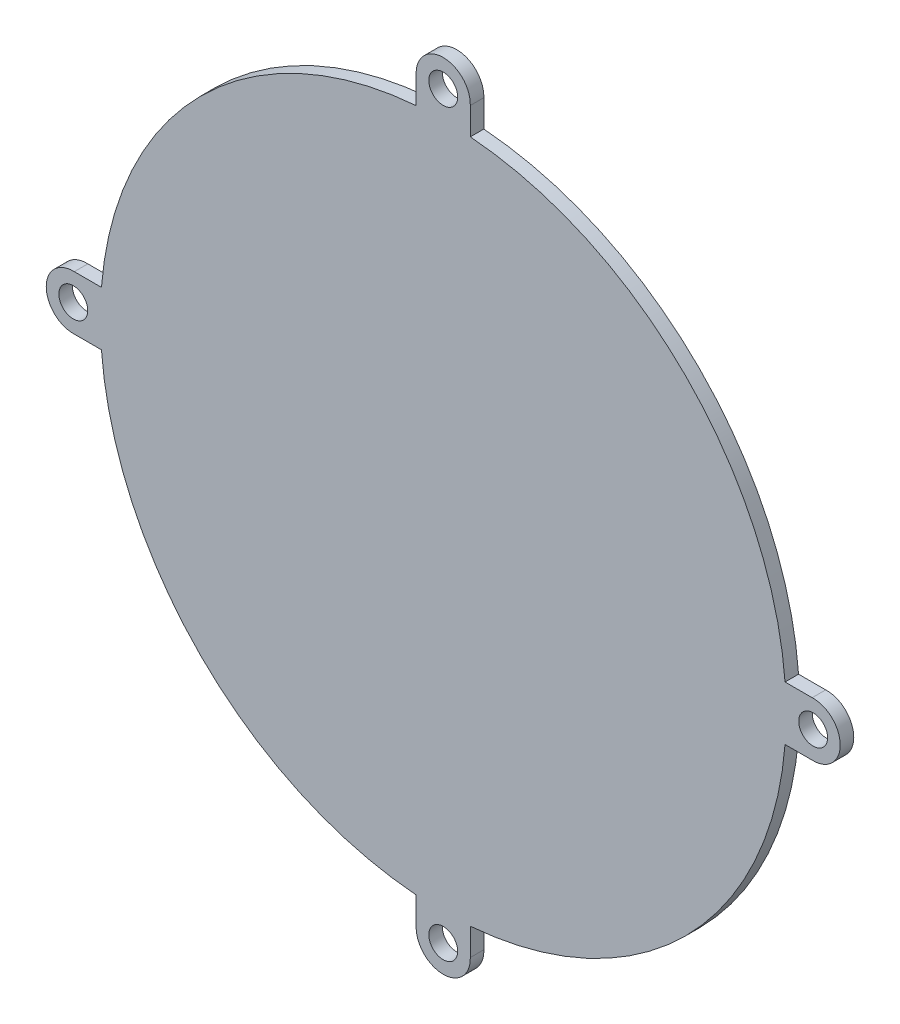
SolidWorks part; units mm, degrees
ref_plane "Front" through (0, 0, 0) normal (0, 0, 1) x (1, 0, 0)
ref_plane "Top" through (0, 0, 0) normal (0, 1, 0) x (1, 0, 0)
ref_plane "Right" through (0, 0, 0) normal (1, 0, 0) x (0, 0, -1)
sketch "Sketch1" plane through (0, 0, 0) normal (0, 0, 1) x (1, 0, 0)
  line L0 (-40.8902, 2.998) -> (-37.8816, 2.998)
  line L1 (40.8902, -2.998) -> (37.8816, -2.998)
  line L2 (-2.998, -40.8902) -> (-2.998, -37.8816)
  line L3 (2.998, 40.8902) -> (2.998, 37.8816)
  line L4 (-37.8816, -2.998) -> (-40.8902, -2.998)
  line L6 (-2.998, 37.8816) -> (-2.998, 40.8902)
  line L8 (37.8816, 2.998) -> (40.8902, 2.998)
  line L10 (2.998, -37.8816) -> (2.998, -40.8902)
  arc A1 (-37.8816, -2.998) -> (-2.998, -37.8816) centre (0, 0) ccw
  arc A2 (2.998, 40.8902) -> (-2.998, 40.8902) centre (0, 41) ccw
  circle A3 centre (0, 41) radius 1.6
  circle A4 centre (41, 0) radius 1.6
  arc A5 (40.8902, -2.998) -> (40.8902, 2.998) centre (41, 0) ccw
  circle A6 centre (0, -41) radius 1.6
  arc A7 (-2.998, -40.8902) -> (2.998, -40.8902) centre (0, -41) ccw
  circle A8 centre (-41, 0) radius 1.6
  arc A9 (-40.8902, 2.998) -> (-40.8902, -2.998) centre (-41, 0) ccw
  arc A13 (2.998, -37.8816) -> (37.8816, -2.998) centre (0, 0) ccw
  arc A14 (37.8816, 2.998) -> (2.998, 37.8816) centre (0, 0) ccw
  arc A15 (-2.998, 37.8816) -> (-37.8816, 2.998) centre (0, 0) ccw
  dimension "D1" = 4
extrude "Boss-Extrude1" add sketch "Sketch1" along normal blind 1.5
